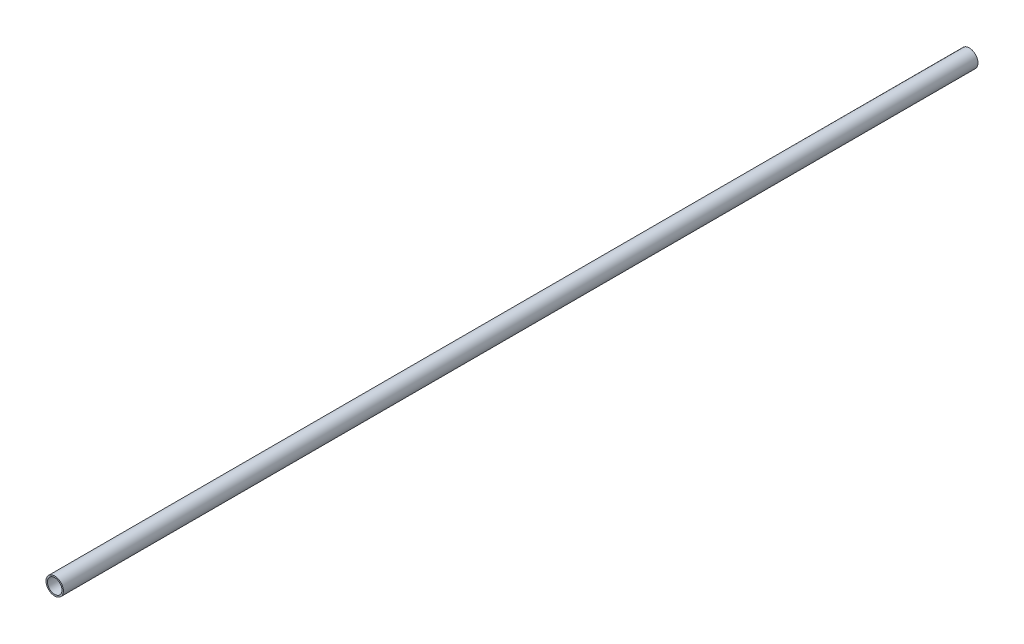
SolidWorks part; units mm, degrees
material "McMaster Carbon Fiber Twill Tube"
ref_plane "Front Plane" through (0, 0, 0) normal (0, 0, 1) x (1, 0, 0)
ref_plane "Top Plane" through (0, 0, 0) normal (0, 1, 0) x (1, 0, 0)
ref_plane "Right Plane" through (0, 0, 0) normal (1, 0, 0) x (0, 0, -1)
sketch "Sketch1" plane through (0, 0, 0) normal (0, 0, 1) x (1, 0, 0)
  circle A0 centre (0, 0) radius 9.525
  circle A1 centre (0, 0) radius 7.9375
  dimension "D1" = 19.05
  dimension "D2" = 1.5875
extrude "Boss-Extrude1" add sketch "Sketch1" along normal blind 1000.125
